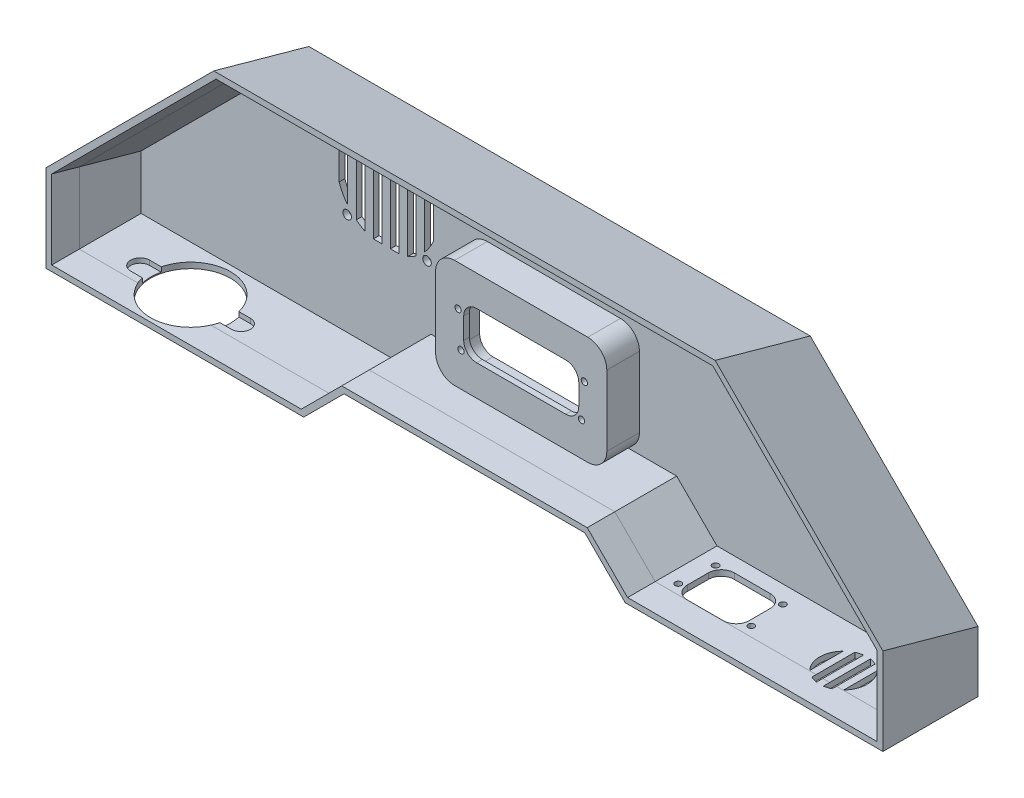
SolidWorks part; units mm, degrees
material "ABS PC"
ref_plane "Front Plane" through (0, 0, 0) normal (0, 0, 1) x (1, 0, 0)
ref_plane "Top Plane" through (0, 0, 0) normal (0, 1, 0) x (1, 0, 0)
ref_plane "Right Plane" through (0, 0, 0) normal (1, 0, 0) x (0, 0, -1)
sketch "Sketch1" plane through (0, 0, 0) normal (0, 0, 1) x (1, 0, 0)
  line L0 (-135.1127, 0) -> (135.1127, 0) construction
  line L1 (-135.1127, 0) -> (-228, -92.8873) construction
  line L2 (-228, -92.8873) -> (-228, -150) construction
  line L3 (-228, -150) -> (-81.2132, -150) construction
  line L5 (-81.2132, -150) -> (-60, -128.7868) construction
  line L6 (-60, -128.7868) -> (60, -128.7868) construction
  line L7 (60, -128.7868) -> (81.2132, -150) construction
  line L8 (81.2132, -150) -> (228, -150) construction
  line L9 (135.1127, 0) -> (228, -92.8873) construction
  line L10 (228, -92.8873) -> (228, -150) construction
  line L16 (-131.799, -8) -> (131.799, -8)
  line L17 (131.799, -8) -> (220, -96.201)
  line L18 (220, -96.201) -> (220, -142)
  line L19 (84.5269, -142) -> (220, -142)
  line L20 (63.3137, -120.7868) -> (84.5269, -142)
  line L21 (-63.3137, -120.7868) -> (63.3137, -120.7868)
  line L22 (-84.5269, -142) -> (-63.3137, -120.7868)
  line L23 (-220, -142) -> (-84.5269, -142)
  line L24 (-220, -96.201) -> (-220, -142)
  line L25 (-131.799, -8) -> (-220, -96.201)
  point P2 (0, 0)
  dimension "D1" = 120
  dimension "D2" = 30
  dimension "D3" = 150
  dimension "D4" = 270.2254
  dimension "D5" = 131.3625
  dimension "D6" = 8
ref_plane "Plane1" through (0, 0, -50) normal (0, 0, 1) x (1, 0, 0)
sketch "Sketch2" plane through (0, 0, -50) normal (0, 0, 1) x (1, 0, 0)
  line L15 (81.2132, -150) -> (228, -150) construction
  line L16 (60, -128.7868) -> (81.2132, -150) construction
  line L17 (-60, -128.7868) -> (60, -128.7868) construction
  line L18 (-81.2132, -150) -> (-60, -128.7868) construction
  line L19 (-228, -150) -> (-81.2132, -150) construction
  line L20 (81.2132, -150) -> (228, -150) construction
  line L21 (60, -128.7868) -> (81.2132, -150) construction
  line L22 (-60, -128.7868) -> (60, -128.7868) construction
  line L23 (-81.2132, -150) -> (-60, -128.7868) construction
  line L24 (-228, -150) -> (-81.2132, -150) construction
  line L25 (-228, -150) -> (-228, -106.7708) construction
  line L26 (-228, -106.7708) -> (-135.1127, -13.8835) construction
  line L27 (-135.1127, -13.8835) -> (135.1127, -13.8835) construction
  line L28 (135.1127, -13.8835) -> (228, -106.7708) construction
  line L29 (228, -106.7708) -> (228, -150) construction
  line L30 (84.5269, -142) -> (220, -142)
  line L31 (220, -110.0845) -> (220, -142)
  line L32 (131.799, -21.8835) -> (220, -110.0845)
  line L33 (-131.799, -21.8835) -> (131.799, -21.8835)
  line L34 (-220, -110.0845) -> (-131.799, -21.8835)
  line L35 (-220, -142) -> (-220, -110.0845)
  line L36 (-220, -142) -> (-84.5269, -142)
  line L37 (-84.5269, -142) -> (-63.3137, -120.7868)
  line L38 (-63.3137, -120.7868) -> (63.3137, -120.7868)
  line L39 (63.3137, -120.7868) -> (84.5269, -142)
  dimension "D1" = 43.2292
  dimension "D2" = 135
  dimension "D3" = 131.3625
  dimension "D4" = 8
loft "Loft1" add profiles "Sketch1", "Sketch2"
shell "Shell1" thickness 3
sketch "Sketch3" plane through (0, -139, 5.433) normal (0, 1, 0) x (1, 0, 0)
  line L0 (112, 44.733) -> (112, 20.033) construction
  line L1 (94.3, 43.133) -> (112, 43.133) construction
  line L2 (112, 43.133) -> (129.7, 43.133) construction
  line L3 (92.8, 25.033) -> (112, 25.033) construction
  line L4 (112, 25.033) -> (131.2, 25.033) construction
  line L5 (85.7696, 5.433) -> (217, 5.433) construction
  line L6 (102.55, 44.733) -> (121.45, 44.733)
  line L7 (95.75, 37.933) -> (95.75, 26.833)
  line L8 (102.55, 20.033) -> (121.45, 20.033)
  line L9 (128.25, 37.933) -> (128.25, 26.833)
  line L10 (112, 20.033) -> (112, 44.733) construction
  line L11 (95.75, 32.383) -> (128.25, 32.383) construction
  line L14 (217, 5.433) -> (217, 52.433) construction
  circle A0 centre (94.3, 43.133) radius 1.65
  circle A1 centre (129.7, 43.133) radius 1.65
  circle A2 centre (92.8, 25.033) radius 1.65
  circle A3 centre (131.2, 25.033) radius 1.65
  arc A4 (95.75, 26.833) -> (102.55, 20.033) centre (102.55, 26.833) ccw
  arc A5 (121.45, 20.033) -> (128.25, 26.833) centre (121.45, 26.833) ccw
  arc A6 (128.25, 37.933) -> (121.45, 44.733) centre (121.45, 37.933) ccw
  arc A7 (102.55, 44.733) -> (95.75, 37.933) centre (102.55, 37.933) ccw
  point P10 (112, 32.383)
  point P19 (95.75, 20.033)
  point P22 (128.25, 20.033)
  point P25 (128.25, 44.733)
  dimension "D1" = 3.3
  dimension "D3" = 35.4
  dimension "D6" = 5
  dimension "D8" = 6.8
  dimension "D2" = 38.4
  dimension "D4" = 24.7
  dimension "D5" = 32.5
  dimension "D7" = 18.1
  dimension "D9" = 14.6
  dimension "D10" = 88.75
extrude "Cut-Extrude1" cut sketch "Sketch3" against normal through all
sketch "Sketch4" plane through (0, 0, -47) normal (0, 0, 1) x (1, 0, 0)
  line L0 (-112.8831, -64.3996) -> (-62.4831, -64.3996)
  line L1 (-87.6831, -39.2496) -> (-87.6831, -89.5496) construction
  line L2 (-112.8831, -64.3996) -> (-62.4831, -64.3996) construction
  line L3 (-87.6831, -89.5496) -> (-87.6831, -39.2496)
  line L4 (-96.0334, -39.2496) -> (-79.3328, -39.2496)
  line L5 (-62.4831, -56.2014) -> (-62.4831, -72.5977)
  line L6 (-96.0334, -89.5496) -> (-79.3328, -89.5496)
  line L7 (-112.8831, -56.2014) -> (-112.8831, -72.5977)
  line L8 (-112.8831, -33.6139) -> (-112.8831, -104.5592)
  line L9 (-108.3831, -33.6139) -> (-108.3831, -104.5592)
  line L10 (-103.8831, -33.6139) -> (-103.8831, -104.5592)
  line L11 (-99.3831, -33.6139) -> (-99.3831, -104.5592)
  line L12 (-94.8831, -33.6139) -> (-94.8831, -104.5592)
  line L13 (-90.3831, -33.6139) -> (-90.3831, -104.5592)
  line L14 (-85.8831, -33.6139) -> (-85.8831, -104.5592)
  line L15 (-81.3831, -33.6139) -> (-81.3831, -104.5592)
  line L16 (-76.8831, -33.6139) -> (-76.8831, -104.5592)
  line L17 (-72.3831, -33.6139) -> (-72.3831, -104.5592)
  line L18 (-67.8831, -33.6139) -> (-67.8831, -104.5592)
  line L19 (-63.3831, -33.6139) -> (-63.3831, -104.5592)
  circle A0 centre (-108.6831, -43.3996) radius 2.25
  circle A1 centre (-66.6831, -43.3996) radius 2.25
  circle A2 centre (-66.6831, -85.3996) radius 2.25
  circle A3 centre (-108.6831, -85.3996) radius 2.25
  arc A4 (-112.8831, -72.5977) -> (-96.0334, -89.5496) centre (-87.6831, -64.3996) ccw
  arc A5 (-96.0334, -39.2496) -> (-112.8831, -56.2014) centre (-87.6831, -64.3996) ccw
  arc A6 (-79.3328, -89.5496) -> (-62.4831, -72.5977) centre (-87.6831, -64.3996) ccw
  arc A7 (-62.4831, -56.2014) -> (-79.3328, -39.2496) centre (-87.6831, -64.3996) ccw
  point P12 (-87.6831, -64.3996)
  point P15 (-87.6831, -64.3996)
  dimension "D3" = 50.4
  dimension "D1" = 4.5
  dimension "D2" = 42
extrude "Cut-Extrude2" cut sketch "Sketch4" against normal through all contours L9 A5 L7 L0 | L7 A4 L9 L0 | L11 A5 L10 L0 | L10 A4 L11 L0 | L13 L4 L12 L0 | L13 L0 L12 L6 | L15 L4 L14 L0 | L15 L0 L14 L6 | L17 A7 L16 L0 | L16 A6 L17 L0 | L19 A7 L18 L0 | L18 A6 L19 L0 | A0 | A1 | A2 | A3
sketch "Sketch6" plane through (0, 0, -47) normal (0, 0, 1) x (1, 0, 0)
  line L1 (-35, -60.7868) -> (35, -60.7868)
  line L2 (-45, -70.7868) -> (-45, -107.7868)
  line L3 (-35, -117.7868) -> (35, -117.7868)
  line L4 (45, -70.7868) -> (45, -107.7868)
  line L5 (0, -117.7868) -> (0, -60.7868) construction
  line L6 (-45, -89.2868) -> (45, -89.2868) construction
  line L7 (-64.5563, -117.7868) -> (64.5563, -117.7868) construction
  arc A0 (-45, -107.7868) -> (-35, -117.7868) centre (-35, -107.7868) ccw
  arc A1 (45, -107.7868) -> (35, -117.7868) centre (35, -107.7868) cw
  arc A2 (45, -70.7868) -> (35, -60.7868) centre (35, -70.7868) ccw
  arc A3 (-35, -60.7868) -> (-45, -70.7868) centre (-35, -70.7868) ccw
  point P0 (0, -89.2868)
  point P5 (0, -89.2868)
  point P11 (45, -117.7868)
  point P14 (45, -60.7868)
  point P18 (-45, -60.7868)
  point P24 (0, -117.7868)
  dimension "D3" = 10
  dimension "D1" = 90
  dimension "D2" = 57
extrude "Boss-Extrude1" add sketch "Sketch6" along normal blind 17.15
sketch "Sketch8" plane through (0, 0, -50) normal (0, 0, -1) x (-1, 0, 0)
  line L0 (-42, -70.7868) -> (-42, -107.7868)
  line L1 (-35, -114.7868) -> (35, -114.7868)
  line L2 (42, -107.7868) -> (42, -70.7868)
  line L3 (35, -63.7868) -> (-35, -63.7868)
  line L4 (35, -60.7868) -> (-35, -60.7868)
  line L5 (45, -107.7868) -> (45, -70.7868)
  line L6 (-131.799, -21.8835) -> (-220, -110.0845)
  line L7 (-131.799, -21.8835) -> (-220, -110.0845)
  line L8 (-220, -110.0845) -> (-220, -142)
  line L9 (-220, -110.0845) -> (-220, -142)
  line L10 (-220, -142) -> (-84.5269, -142)
  line L11 (-220, -142) -> (-84.5269, -142)
  line L12 (-84.5269, -142) -> (-63.3137, -120.7868)
  line L13 (-84.5269, -142) -> (-63.3137, -120.7868)
  line L14 (-63.3137, -120.7868) -> (63.3137, -120.7868)
  line L15 (-63.3137, -120.7868) -> (63.3137, -120.7868)
  line L16 (63.3137, -120.7868) -> (84.5269, -142)
  line L17 (63.3137, -120.7868) -> (84.5269, -142)
  line L18 (-35, -117.7868) -> (35, -117.7868)
  line L19 (-45, -70.7868) -> (-45, -107.7868)
  line L20 (35, -60.7868) -> (-35, -60.7868) construction
  line L21 (45, -107.7868) -> (45, -70.7868) construction
  line L22 (-35, -117.7868) -> (35, -117.7868) construction
  line L23 (-45, -70.7868) -> (-45, -107.7868) construction
  line L34 (84.5269, -142) -> (220, -142)
  line L35 (84.5269, -142) -> (220, -142)
  line L36 (220, -142) -> (220, -110.0845)
  line L37 (220, -142) -> (220, -110.0845)
  line L38 (220, -110.0845) -> (131.799, -21.8835)
  line L39 (220, -110.0845) -> (131.799, -21.8835)
  line L40 (131.799, -21.8835) -> (-131.799, -21.8835)
  line L41 (131.799, -21.8835) -> (-131.799, -21.8835)
  arc A0 (-42, -107.7868) -> (-35, -114.7868) centre (-35, -107.7868) ccw
  arc A1 (35, -114.7868) -> (42, -107.7868) centre (35, -107.7868) ccw
  arc A2 (42, -70.7868) -> (35, -63.7868) centre (35, -70.7868) ccw
  arc A3 (-35, -63.7868) -> (-42, -70.7868) centre (-35, -70.7868) ccw
  arc A4 (-35, -60.7868) -> (-45, -70.7868) centre (-35, -70.7868) ccw
  arc A5 (-35, -60.7868) -> (-45, -70.7868) centre (-35, -70.7868) ccw
  arc A6 (-45, -107.7868) -> (-35, -117.7868) centre (-35, -107.7868) ccw
  arc A7 (-45, -107.7868) -> (-35, -117.7868) centre (-35, -107.7868) ccw
  arc A8 (35, -117.7868) -> (45, -107.7868) centre (35, -107.7868) ccw
  arc A9 (35, -117.7868) -> (45, -107.7868) centre (35, -107.7868) ccw
  arc A10 (45, -70.7868) -> (35, -60.7868) centre (35, -70.7868) ccw
  arc A11 (45, -70.7868) -> (35, -60.7868) centre (35, -70.7868) ccw
  dimension "D1" = 0
  dimension "D2" = 0
  dimension "D3" = 3
extrude "Cut-Extrude3" cut sketch "Sketch8" against normal blind 17.15
sketch "Sketch9" plane through (0, 0, -32.85) normal (0, 0, -1) x (-1, 0, 0)
  line L0 (0, -63.7868) -> (0, -114.7868) construction
  line L1 (35, -63.7868) -> (-35, -63.7868) construction
  line L2 (-35, -114.7868) -> (35, -114.7868) construction
  line L3 (-33.2, -81.9368) -> (0, -81.9368) construction
  line L4 (0, -81.9368) -> (33.2, -81.9368) construction
  line L5 (-31.7, -100.0368) -> (0, -100.0368) construction
  line L6 (0, -100.0368) -> (31.7, -100.0368) construction
  line L8 (-23.45, -76.9368) -> (23.45, -76.9368)
  line L9 (-30.25, -83.7368) -> (-30.25, -94.8368)
  line L10 (-23.45, -101.6368) -> (23.45, -101.6368)
  line L11 (30.25, -83.7368) -> (30.25, -94.8368)
  line L12 (0, -101.6368) -> (0, -76.9368) construction
  line L13 (-30.25, -89.2868) -> (30.25, -89.2868) construction
  circle A0 centre (-33.2, -81.9368) radius 1.65
  circle A1 centre (-31.7, -100.0368) radius 1.65
  circle A2 centre (33.2, -81.9368) radius 1.65
  circle A3 centre (31.7, -100.0368) radius 1.65
  arc A4 (-30.25, -94.8368) -> (-23.45, -101.6368) centre (-23.45, -94.8368) ccw
  arc A5 (30.25, -94.8368) -> (23.45, -101.6368) centre (23.45, -94.8368) cw
  arc A6 (30.25, -83.7368) -> (23.45, -76.9368) centre (23.45, -83.7368) ccw
  arc A7 (-23.45, -76.9368) -> (-30.25, -83.7368) centre (-23.45, -83.7368) ccw
  point P9 (0, -89.2868)
  point P22 (-30.25, -101.6368)
  point P25 (30.25, -101.6368)
  point P28 (30.25, -76.9368)
  point P32 (0, -89.2868)
  dimension "D2" = 3.3
  dimension "D8" = 6.8
  dimension "D1" = 66.4
  dimension "D3" = 18.1
  dimension "D4" = 60.5
  dimension "D5" = 24.7
  dimension "D6" = 63.4
  dimension "D7" = 5
extrude "Cut-Extrude4" cut sketch "Sketch9" against normal up to surface (3 mm away) up to face at (0, -89.2868, -29.85)
ref_plane "Plane2" through (0, 0, -14.5) normal (0, 0, 1) x (1, 0, 0)
sketch "Sketch10" plane through (0, -139, 0) normal (0, 1, 0) x (1, 0, 0)
  line L0 (85.7696, 0) -> (85.7696, 47) construction
  line L1 (166.841, 14.7518) -> (166.841, 32.2482)
  line L2 (170.4124, 34.7938) -> (170.4124, 12.2062)
  line L3 (173.9838, 11.1282) -> (173.9838, 35.8718)
  line L4 (177.5553, 35.8718) -> (177.5553, 11.1282)
  line L5 (181.1267, 12.2062) -> (181.1267, 34.7938)
  line L6 (184.6981, 32.2482) -> (184.6981, 14.7518)
  line L7 (163.2696, 23.5) -> (166.841, 23.5) construction
  line L8 (166.841, 23.5) -> (170.4124, 23.5) construction
  line L9 (170.4124, 23.5) -> (173.9838, 23.5) construction
  line L10 (173.9838, 23.5) -> (177.5553, 23.5) construction
  line L11 (177.5553, 23.5) -> (181.1267, 23.5) construction
  line L12 (181.1267, 23.5) -> (184.6981, 23.5) construction
  line L13 (184.6981, 23.5) -> (188.2696, 23.5) construction
  circle A0 centre (175.7696, 23.5) radius 12.5
  point P6 (85.7696, 23.5)
  point P19 (166.841, 23.5)
  point P20 (170.4124, 23.5)
  point P21 (173.9838, 23.5)
  point P22 (177.5553, 23.5)
  point P23 (181.1267, 23.5)
  point P24 (184.6981, 23.5)
  dimension "D1" = 25
  dimension "D2" = 90
extrude "Cut-Extrude5" cut sketch "Sketch10" against normal up to surface (3 mm away) contours L1 A0 | L3 A0 L2 | L4 A0 L5 | L6 A0 up to face at (112, -142, -26.95)
sketch "Sketch11" plane through (0, -139, 0) normal (0, 1, 0) x (1, 0, 0)
  line L6 (-217, 0) -> (-85.7696, 0) construction
  line L7 (-217, 0) -> (-217, 47) construction
  circle A0 centre (-167, 23) radius 21
  point P6 (-217, 23.5)
  dimension "D1" = 42
  dimension "D2" = 23
  dimension "D3" = 50
split line "Split Line2"
sketch "Sketch12" plane through (0, 0, -14.5) normal (0, 0, 1) x (1, 0, 0)
  line L0 (-85.7696, -139) -> (-217, -139)
  line L1 (-217, -139) -> (-217, -101.5509)
  line L2 (-217, -101.5509) -> (-130.5888, -15.1397)
  line L3 (-130.5888, -15.1397) -> (130.5888, -15.1397)
  line L4 (130.5888, -15.1397) -> (217, -101.5509)
  line L5 (217, -101.5509) -> (217, -139)
  line L6 (217, -139) -> (85.7696, -139)
  line L7 (85.7696, -139) -> (64.5563, -117.7868)
  line L8 (64.5563, -117.7868) -> (-64.5563, -117.7868)
  line L9 (-64.5563, -117.7868) -> (-85.7696, -139)
  line L10 (-86.8217, -136.46) -> (-214.46, -136.46)
  line L11 (-214.46, -136.46) -> (-214.46, -102.603)
  line L12 (-214.46, -102.603) -> (-129.5367, -17.6797)
  line L13 (-129.5367, -17.6797) -> (129.5367, -17.6797)
  line L14 (129.5367, -17.6797) -> (214.46, -102.603)
  line L15 (214.46, -102.603) -> (214.46, -136.46)
  line L16 (214.46, -136.46) -> (86.8217, -136.46)
  line L17 (86.8217, -136.46) -> (65.6085, -115.2468)
  line L18 (65.6085, -115.2468) -> (-65.6085, -115.2468)
  line L19 (-65.6085, -115.2468) -> (-86.8217, -136.46)
  circle A1 centre (-31.7, -100.0368) radius 1.65 construction
  circle A3 centre (31.7, -100.0368) radius 1.65 construction
  circle A6 centre (33.2, -81.9368) radius 1.65 construction
  circle A7 centre (-33.2, -81.9368) radius 1.65 construction
  circle A9 centre (-31.7, -100.0368) radius 1.65
  circle A10 centre (31.7, -100.0368) radius 1.65
  circle A11 centre (33.2, -81.9368) radius 1.65
  circle A12 centre (-33.2, -81.9368) radius 1.65
  circle A14 centre (-189.2634, -120.2634) radius 7.5
  circle A16 centre (-149.2634, -120.2634) radius 7.5
  circle A18 centre (-109.2634, -120.2634) radius 7.5
  circle A20 centre (-22.5, -33.7366) radius 2.5
  circle A22 centre (-7.5, -33.7366) radius 2.5
  circle A24 centre (7.5, -33.7366) radius 2.5
  circle A26 centre (22.5, -33.7366) radius 2.5
  circle A28 centre (121.2634, -55.2634) radius 10
  circle A30 centre (151.2634, -120.2634) radius 9
  circle A32 centre (196.2634, -120.2634) radius 9
  dimension "D1" = 2.54
extrude "Cut-Extrude9" cut sketch "Sketch11" against normal up to surface (3 mm away) up to face at (-186.1317, -142, -12.5)
sketch "Sketch15" plane through (0, -139, 0) normal (0, 1, 0) x (1, 0, 0)
  line L0 (-188, 28) -> (-188, 18)
  line L1 (-188, 28) -> (-187.3961, 28)
  line L2 (-188, 18) -> (-187.3961, 18)
  line L3 (-188, 28) -> (-193.5, 28)
  line L4 (-188, 18) -> (-193.5, 18)
  line L5 (-167, 2) -> (-167, 44) construction
  line L6 (-146, 18) -> (-140.5, 18)
  line L7 (-146, 28) -> (-140.5, 28)
  line L8 (-146, 18) -> (-146.6039, 18)
  line L9 (-146, 28) -> (-146.6039, 28)
  line L10 (-146, 28) -> (-146, 18)
  circle A0 centre (-167, 23) radius 21 construction
  circle A1 centre (-167, 23) radius 21
  circle A2 centre (-193.5, 23) radius 5
  circle A3 centre (-140.5, 23) radius 5
  point P6 (-188, 23)
  point P22 (-146, 23)
  dimension "D1" = 10
  dimension "D2" = 5.5
extrude "Cut-Extrude10" cut sketch "Sketch15" against normal blind 2.46 contours A2 L4 L0 L3 | A2 | A3 | L6 A3 L7 L10 | A1 L8 L10 | A1 L10 L9 | A1 L0 L2 | A1 L1 L0
